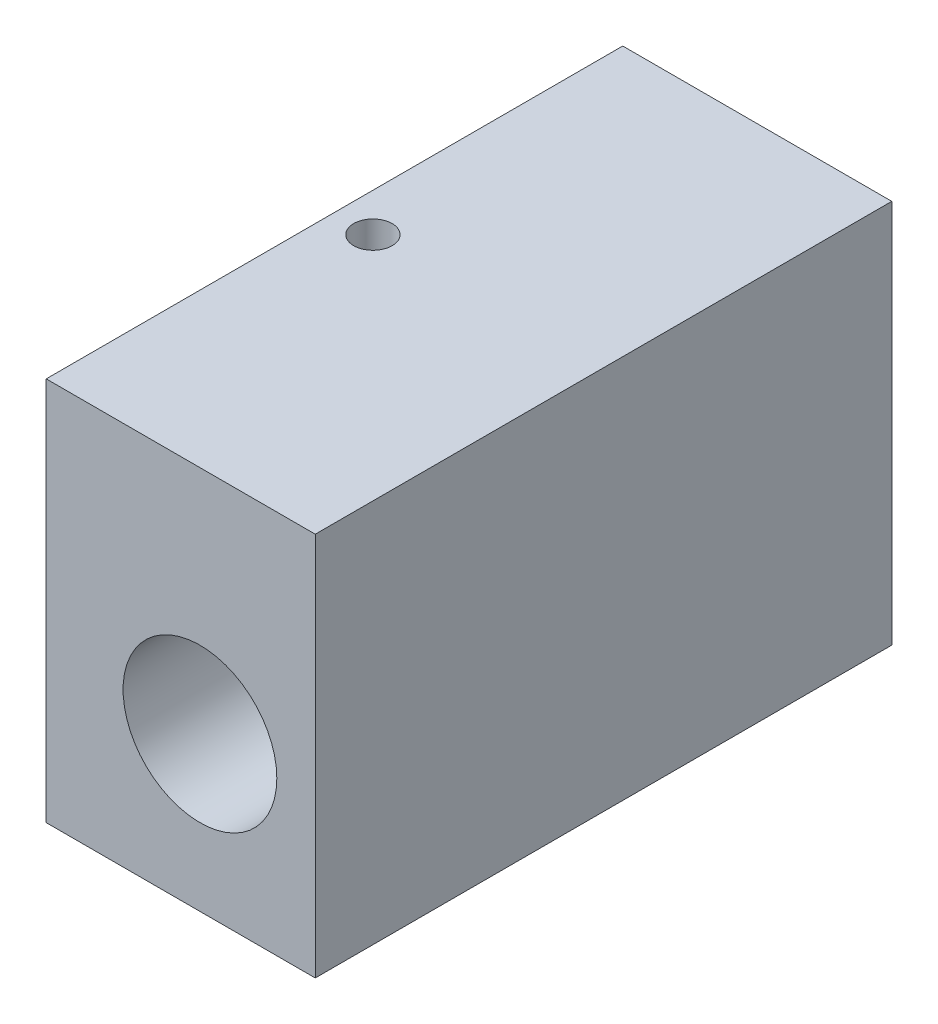
SolidWorks part; units mm, degrees
ref_plane "前视基准面" through (0, 0, 0) normal (0, 0, 1) x (1, 0, 0)
ref_plane "上视基准面" through (0, 0, 0) normal (0, 1, 0) x (1, 0, 0)
ref_plane "右视基准面" through (0, 0, 0) normal (1, 0, 0) x (0, 0, -1)
sketch "草图1" plane through (0, 0, 0) normal (0, 1, 0) x (1, 0, 0)
  line L1 (0, 0) -> (7, 0)
  line L2 (0, 0) -> (0, 15)
  line L3 (0, 15) -> (7, 15)
  line L4 (7, 0) -> (7, 15)
  dimension "D1" = 15
  dimension "D2" = 7
extrude "凸台-拉伸1" add sketch "草图1" along normal blind 10
sketch "草图2" plane through (0, 0, 0) normal (0, 0, 1) x (1, 0, 0)
  line L0 (0, 10) -> (0, 0) construction
  line L1 (0, 0) -> (7, 0) construction
  circle A0 centre (4, 4) radius 2
  point P6 (5.9623, 2.0291)
  dimension "D1" = 4
  dimension "D3" = 4
  dimension "D2" = 4
extrude "切除-拉伸1" cut sketch "草图2" against normal through all
sketch "草图3" plane through (0, 10, 0) normal (0, 1, 0) x (1, 0, 0)
  line L0 (0, 15) -> (0, 0) construction
  line L1 (0, 0) -> (7, 0) construction
  circle A0 centre (1, 7.5) radius 0.5
  dimension "D1" = 1
  dimension "D3" = 1
  dimension "D2" = 7.5
extrude "切除-拉伸2" cut sketch "草图3" against normal blind 8
